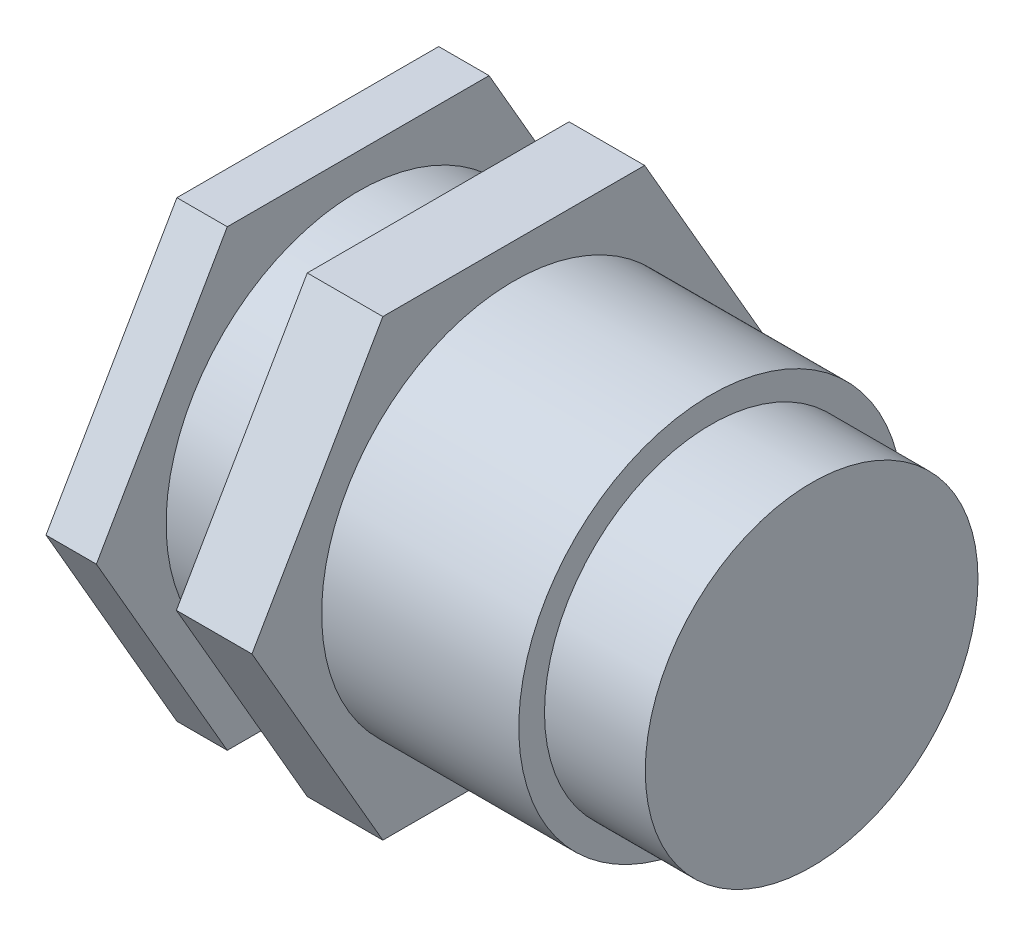
SolidWorks part; units mm, degrees
ref_plane "Front Plane" through (0, 0, 0) normal (0, 0, 1) x (1, 0, 0)
ref_plane "Top Plane" through (0, 0, 0) normal (0, 1, 0) x (1, 0, 0)
ref_plane "Right Plane" through (0, 0, 0) normal (1, 0, 0) x (0, 0, -1)
sketch "Sketch1" plane through (0, 0, 0) normal (1, 0, 0) x (0, 0, -1)
  line L1 (5.1962, 9) -> (-5.1962, 9)
  line L2 (-5.1962, 9) -> (-10.3923, 0)
  line L3 (-10.3923, 0) -> (-5.1962, -9)
  line L4 (-5.1962, -9) -> (5.1962, -9)
  line L5 (5.1962, -9) -> (10.3923, 0)
  line L6 (10.3923, 0) -> (5.1962, 9)
  circle A0 centre (0, 0) radius 9 construction
  point P1 (14.2498, 24.6814)
  dimension "D1" = 18
extrude "Boss-Extrude1" add sketch "Sketch1" along normal blind 2
sketch "Sketch2" plane through (2, 0, 0) normal (1, 0, 0) x (0, 0, -1)
  circle A0 centre (0, 0) radius 7.625
  dimension "D1" = 15.25
extrude "Boss-Extrude2" add sketch "Sketch2" along normal blind 14
sketch "Sketch3" plane through (16, 0, 0) normal (1, 0, 0) x (0, 0, -1)
  circle A0 centre (0, 0) radius 6.604
  dimension "D1" = 13.208
extrude "Boss-Extrude3" add sketch "Sketch3" along normal offset from surface (4 mm away) 20 up to face at (0, 0, 0)
sketch "Sketch4" plane through (2, 0, 0) normal (1, 0, 0) x (0, 0, -1)
  line L6 (10.3923, 0) -> (5.1962, 9)
  line L7 (5.1962, 9) -> (-5.1962, 9)
  line L8 (-5.1962, 9) -> (-10.3923, 0)
  line L9 (-10.3923, 0) -> (-5.1962, -9)
  line L10 (-5.1962, -9) -> (5.1962, -9)
  line L11 (5.1962, -9) -> (10.3923, 0)
  line L12 (10.3923, 0) -> (5.1962, 9)
  line L13 (5.1962, 9) -> (-5.1962, 9)
  line L14 (-5.1962, 9) -> (-10.3923, 0)
  line L15 (-10.3923, 0) -> (-5.1962, -9)
  line L16 (-5.1962, -9) -> (5.1962, -9)
  line L17 (5.1962, -9) -> (10.3923, 0)
  dimension "D1" = 0
extrude "Boss-Extrude4" add sketch "Sketch4" along normal blind 3 from offset 3.175
equation "\"D1@Sketch1\"=18mm"
